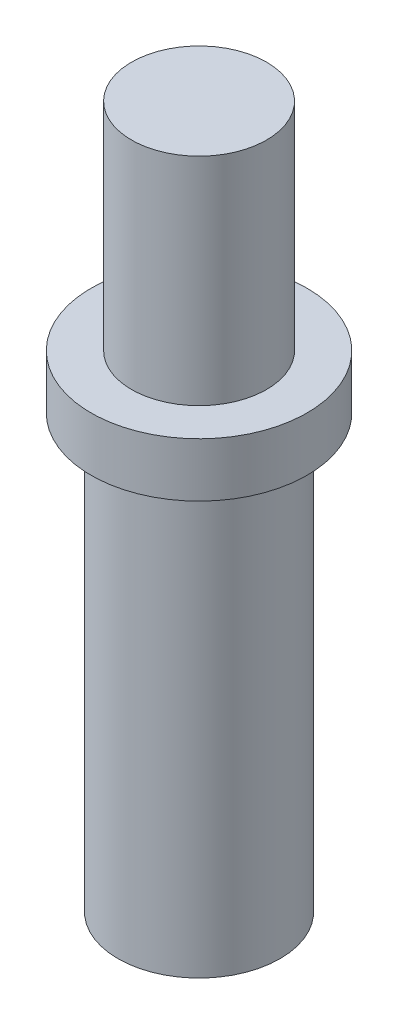
SolidWorks part; units mm, degrees
ref_plane "Plan de face" through (0, 0, 0) normal (0, 0, 1) x (1, 0, 0)
ref_plane "Plan de dessus" through (0, 0, 0) normal (0, 1, 0) x (1, 0, 0)
ref_plane "Plan de droite" through (0, 0, 0) normal (1, 0, 0) x (0, 0, -1)
sketch "Esquisse1" plane through (0, 0, 0) normal (0, 0, 1) x (1, 0, 0)
  line L0 (0, 0) -> (0, 39.4851) construction
  line L1 (4, 27.2297) -> (4, 29.2297)
  line L2 (3, 27.2297) -> (4, 27.2297)
  line L3 (3, 11.2297) -> (3, 27.2297)
  line L4 (2.5, 29.2297) -> (4, 29.2297)
  line L5 (4, 0) -> (4, 39.4851) construction
  line L6 (3, 13.2297) -> (3, 29.2297) construction
  line L7 (2.5, 27.2297) -> (4, 27.2297) construction
  line L8 (4, 13.2297) -> (4, 29.2297) construction
  line L9 (2, 26.2297) -> (2, 11.2297)
  line L10 (2.5, 29.2297) -> (2.5, 37.2297)
  line L11 (0, 26.2297) -> (2, 26.2297)
  line L12 (2, 37.2297) -> (2, 11.2297) construction
  line L13 (2, 11.2297) -> (3, 11.2297)
  line L14 (0, 11.2297) -> (3, 11.2297) construction
  line L15 (0, 37.2297) -> (0, 11.2297) construction
  line L16 (0, 37.2297) -> (0, 26.2297)
  line L17 (0, 37.2297) -> (2.5, 37.2297)
  line L18 (2.5, 37.2297) -> (4, 37.2297) construction
  line L19 (0, 26.2297) -> (3, 26.2297) construction
  dimension "D4" = 8
  dimension "D3" = 2
revolve "Révolution1" add sketch "Esquisse1" angle 360 about L0
